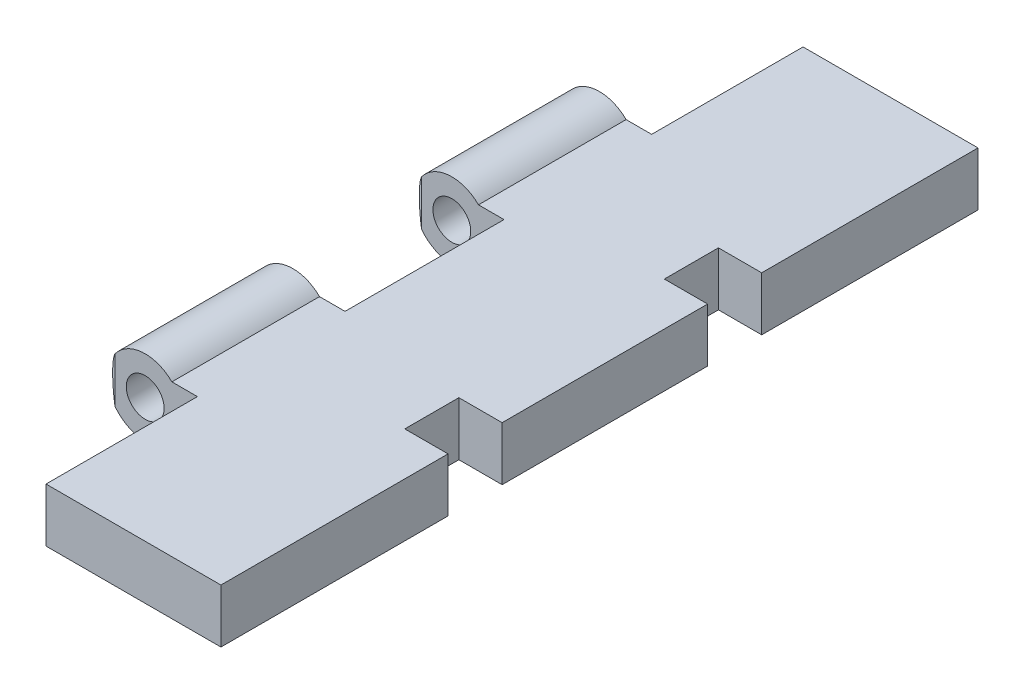
SolidWorks part; units mm, degrees
other "Markup1"
sketch "Sketch35" plane through (-16.5073, 6.25, 100) normal (-0.01, 0.9883, 0.1519) x (0.999, 0.0164, -0.0408)
ref_plane "Front Plane" through (0, 0, 0) normal (0, 0, 1) x (1, 0, 0)
ref_plane "Top Plane" through (0, 0, 0) normal (0, 1, 0) x (1, 0, 0)
ref_plane "Right Plane" through (0, 0, 0) normal (1, 0, 0) x (0, 0, -1)
sketch "Sketch5" plane through (0, 0, 0) normal (0, 1, 0) x (1, 0, 0)
  line L1 (66.8794, 0.0465) -> (96.8794, 0.0465)
  line L2 (66.8794, 0.0465) -> (66.8794, -99.9535)
  line L3 (66.8794, -99.9535) -> (96.8794, -99.9535)
  line L4 (96.8794, 0.0465) -> (96.8794, -99.9535)
  dimension "D1" = 30
extrude "Boss-Extrude2" add sketch "Sketch5" along normal blind 7.1 separate body
sketch "Sketch7" plane through (0, 7.1, 0) normal (0, 1, 0) x (1, 0, 0)
  line L0 (66.8794, 0.0465) -> (73.7744, 0.0465)
  line L2 (73.7744, 0.0465) -> (73.7744, -19.9535)
  line L5 (66.8794, -19.9535) -> (66.8794, 0.0465)
  line L7 (66.8794, -19.9535) -> (73.7744, -19.9535)
  line L10 (66.8794, -60.4535) -> (66.8794, -39.4535)
  line L11 (66.8794, -39.4535) -> (73.7744, -39.4535)
  line L12 (73.7744, -39.4535) -> (73.7744, -60.4535)
  line L15 (66.8794, -60.4535) -> (73.7744, -60.4535)
  line L18 (66.8794, -99.9535) -> (66.8794, -79.9535)
  line L19 (66.8794, -79.9535) -> (73.7744, -79.9535)
  line L20 (73.7744, -79.9535) -> (73.7744, -99.9535)
  line L21 (73.7744, -99.9535) -> (66.8794, -99.9535)
  dimension "D2" = 21
  dimension "D4" = 20
  dimension "D5" = 20
  dimension "D6" = 19.5
  dimension "D7" = 19.5
extrude "Cut-Extrude2" cut sketch "Sketch7" against normal through all
sketch "Sketch8" plane through (66.8794, 0, 0) normal (-1, 0, 0) x (0, 0, 1)
  line L0 (19.9535, 3.55) -> (79.9535, 3.55)
  line L1 (19.9535, 0) -> (19.9535, 7.1) construction
  line L2 (79.9535, 0) -> (79.9535, 7.1) construction
revolve "Revolve-Thin2" add sketch "Sketch8" angle 360 about L0 wall 5
sketch "Sketch9" plane through (0, 7.1, 0) normal (0, 1, 0) x (1, 0, 0)
  line L0 (71.8794, -39.4535) -> (61.8794, -39.4535)
  line L1 (61.8794, -19.9535) -> (61.8794, -79.9535) construction
  line L2 (61.8794, -39.4535) -> (61.8794, -59.9535)
  line L3 (61.8794, -59.9535) -> (71.8794, -59.9535)
  line L4 (71.8794, -59.9535) -> (71.8794, -39.4535)
  line L5 (71.8794, -60.4535) -> (71.8794, -39.4535) construction
  line L6 (73.7744, -39.4535) -> (70.4004, -39.4535) construction
  dimension "D1" = 20.5
  dimension "D2" = 0
split "Split2" trim tools "Sketch9" bodies to split 109 resulting bodies 115
sketch "Sketch10" plane through (0, 0, 79.9535) normal (0, 0, 1) x (1, 0, 0)
  circle A0 centre (66.8794, 3.55) radius 2.5
  circle A1 centre (66.8794, 3.55) radius 5 construction
  dimension "D1" = 0
  dimension "D2" = 5
extrude "Cut-Extrude5" cut sketch "Sketch10" against normal blind 67 and the other way blind 20
sketch "Sketch36" plane through (0, 0, 0) normal (0, 1, 0) x (1, 0, 0)
  line L0 (62.8794, -39.4535) -> (61.8794, -38.7535)
  line L1 (71.8794, -39.4535) -> (61.8794, -39.4535) construction
  line L2 (61.8794, -19.9535) -> (61.8794, -39.4535) construction
  line L3 (61.8794, -38.7535) -> (61.8794, -39.4535)
  line L4 (61.8794, -39.4535) -> (62.8794, -39.4535)
  line L5 (61.8794, -59.9535) -> (71.8794, -59.9535) construction
  line L8 (61.8794, -59.9535) -> (62.8794, -59.9535)
  line L9 (61.8794, -60.6535) -> (61.8794, -59.9535)
  line L10 (62.8794, -59.9535) -> (61.8794, -60.6535)
  line L15 (62.8794, -79.9535) -> (61.8794, -79.2535)
  line L16 (61.8794, -79.2535) -> (61.8794, -79.9535)
  line L17 (61.8794, -79.9535) -> (62.8794, -79.9535)
  line L18 (61.8794, -19.9535) -> (62.8794, -19.9535)
  line L19 (61.8794, -20.6535) -> (61.8794, -19.9535)
  line L20 (62.8794, -19.9535) -> (61.8794, -20.6535)
  dimension "D1" = 1
  dimension "D2" = 0.7
  dimension "D3" = 1
  dimension "D4" = 1
  dimension "D5" = 1
  dimension "D6" = 0
extrude "Cut-Extrude7" cut sketch "Sketch36" against normal through all and the other way through all
sketch "Sketch41" plane through (0, 7.1, 0) normal (0, 1, 0) x (1, 0, 0)
  line L0 (58.1712, -39.4535) -> (73.7744, -39.4535)
  line L1 (58.1712, -39.4535) -> (58.1712, -60.4535)
  line L2 (58.1712, -60.4535) -> (73.7744, -60.4535)
  line L3 (73.7744, -60.4535) -> (73.7744, -39.4535)
  dimension "D2" = 21
extrude "Cut-Extrude9" cut sketch "Sketch41" against normal through all both and the other way through all
scale "Scale1" bodies to scale 147 144 scale about centroid uniform scaling yes scale factor 0.35
sketch "Sketch46" plane through (0, 4.7925, 0) normal (0, 1, 0) x (1, 0, 0)
  line L0 (87.6698, -42.4539) -> (85.6698, -42.4539)
  line L1 (87.6698, -67.4539) -> (87.6698, -32.4539) construction
  line L2 (85.6698, -42.4539) -> (85.6698, -45.4539)
  line L3 (85.6698, -45.4539) -> (87.6698, -45.4539)
  line L4 (87.6698, -49.9539) -> (67.1681, -49.9539) construction
  line L5 (87.6698, -32.4539) -> (79.5831, -32.4539) construction
  line L6 (87.6698, -42.4539) -> (87.6698, -45.4539)
  line L7 (85.6698, -54.4539) -> (87.6698, -54.4539)
  line L8 (87.6698, -57.4539) -> (87.6698, -54.4539)
  line L9 (85.6698, -57.4539) -> (85.6698, -54.4539)
  line L10 (87.6698, -57.4539) -> (85.6698, -57.4539)
  dimension "D1" = 10
  dimension "D2" = 3
  dimension "D3" = 2
extrude "Cut-Extrude10" cut sketch "Sketch46" against normal through all both and the other way through all
sketch "Sketch47" plane through (87.6698, 0, 0) normal (1, 0, 0) x (0, 0, -1)
  line L1 (-57.4539, 4.7925) -> (-56.9539, 4.7925)
  line L2 (-57.4539, 4.7925) -> (-57.4539, 2.3075)
  line L5 (-42.4539, 2.3075) -> (-45.4539, 2.3075) construction
  line L6 (-45.4539, 4.7925) -> (-44.9539, 4.7925)
  line L7 (-45.4539, 4.7925) -> (-45.4539, 2.3075)
  line L9 (-44.9539, 4.7925) -> (-44.9539, 2.3075)
  line L10 (-56.9539, 4.7925) -> (-56.9539, 2.3075)
  line L11 (-60.4539, 2.3075) -> (-53.6289, 2.3075) construction
  line L12 (-56.9539, 2.3075) -> (-57.4539, 2.3075)
  line L13 (-45.4539, 2.3075) -> (-44.9539, 2.3075)
extrude "Boss-Extrude3" add sketch "Sketch47" against normal up to next
